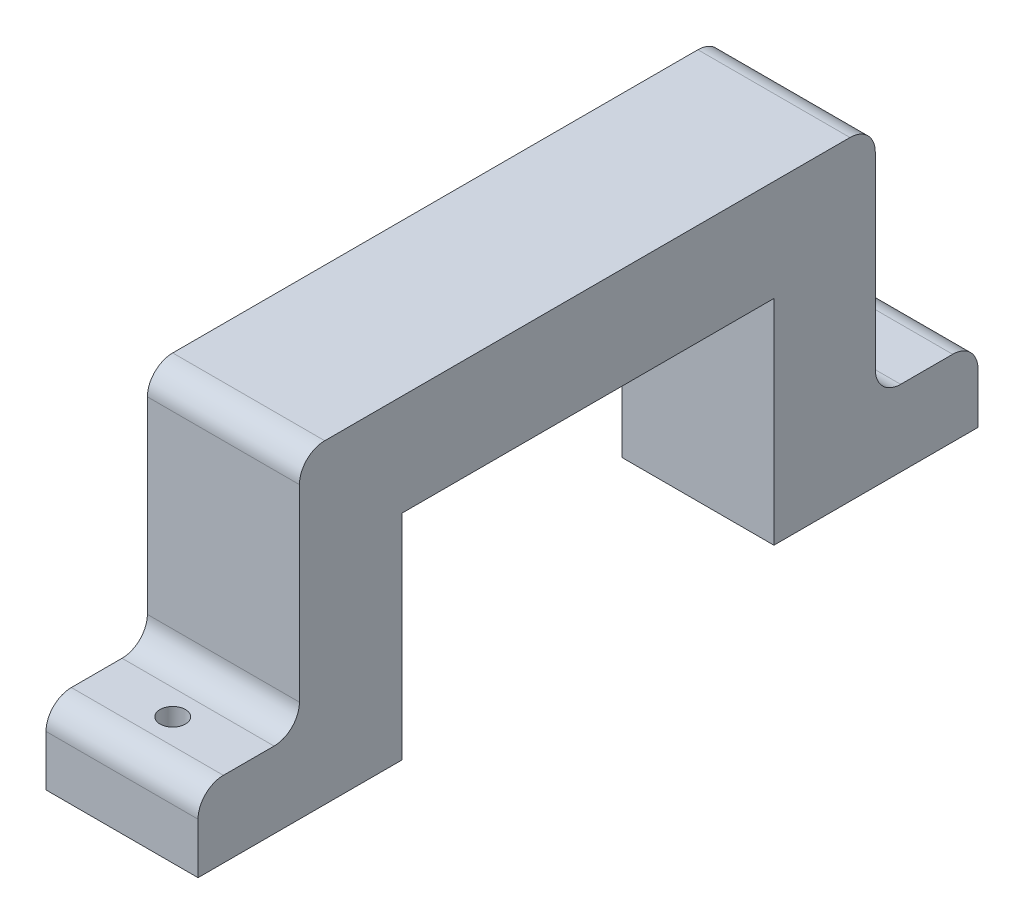
SolidWorks part; units mm, degrees
material "ABS"
ref_plane "Front Plane" through (0, 0, 0) normal (0, 0, 1) x (1, 0, 0)
ref_plane "Top Plane" through (0, 0, 0) normal (0, 1, 0) x (1, 0, 0)
ref_plane "Right Plane" through (0, 0, 0) normal (1, 0, 0) x (0, 0, -1)
sketch "Sketch1" plane through (0, 0, 0) normal (1, 0, 0) x (0, 0, -1)
  line L0 (0, 0) -> (12.7848, 0)
  line L1 (12.7848, 0) -> (12.7848, 13.3902)
  line L2 (12.7848, 13.3902) -> (36.0779, 13.3902)
  line L3 (36.0779, 13.3902) -> (36.0779, 0)
  line L5 (6.351, 19.7402) -> (41.4309, 19.7402)
  line L7 (48.8626, 0) -> (36.0779, 0)
  line L8 (6.351, 19.7402) -> (6.351, 4.7625)
  line L9 (6.351, 4.7625) -> (0, 4.7625)
  line L10 (0, 4.7625) -> (0, 0)
  line L11 (41.4309, 19.7402) -> (42.4279, 19.7402)
  line L12 (42.4279, 19.7402) -> (42.4279, 4.7625)
  line L13 (42.4279, 4.7625) -> (48.8626, 4.7625)
  line L14 (48.8626, 4.7625) -> (48.8626, 0)
  dimension "D1" = 6.35
  dimension "D2" = 12.7848
  dimension "D3" = 12.7848
  dimension "D4" = 0
  dimension "D5" = 13.3902
  dimension "D6" = 23.2931
  dimension "D7" = 35.0799
  dimension "D8" = 6.4338
  dimension "D9" = 4.7625
  dimension "D10" = 4.7625
  dimension "D11" = 6.35
extrude "Boss-Extrude1" add sketch "Sketch1" along normal blind 9.525
ref_plane "Plane2" through (0, 0, -24.4307) normal (0, 0, 1) x (1, 0, 0)
sketch "Sketch2" plane through (0, 4.7625, 0) normal (0, 1, 0) x (1, 0, 0)
  line L0 (0, 48.8626) -> (0, 42.4279) construction
  line L1 (9.525, 48.8626) -> (0, 48.8626) construction
  circle A0 centre (4.7625, 45.6876) radius 0.508
  circle A1 centre (4.7625, 3.1757) radius 0.7938
  dimension "D1" = 4.7625
  dimension "D3" = 42.512
  dimension "D4" = 1.016
  dimension "D2" = 3.175
extrude "Cut-Extrude1" cut sketch "Sketch2" against normal up to next
sketch "Sketch3" plane through (0, 0, 0) normal (-1, 0, 0) x (0, 0, 1)
  line L0 (-36.0779, 0) -> (-48.8626, 0) construction
  line L1 (-36.0779, 13.3902) -> (-36.0779, 0) construction
  circle A0 centre (-38.3232, 6.6853) radius 0.508
  circle A1 centre (-10.5229, 6.6951) radius 0.508
  dimension "D3" = 1.016
  dimension "D1" = 6.6853
  dimension "D2" = 2.2454
  dimension "D4" = 27.8003
extrude "Cut-Extrude2" cut sketch "Sketch3" against normal blind 6.35
fillet "Fillet1" radius 1.5875 6 edges at (4.7625, 4.7625, 0) (4.7625, 4.7625, -6.351) (4.7625, 19.7402, -6.351) (4.7625, 19.7402, -42.4279) (4.7625, 4.7625, -48.8626) (4.7625, 4.7625, -42.4279)
